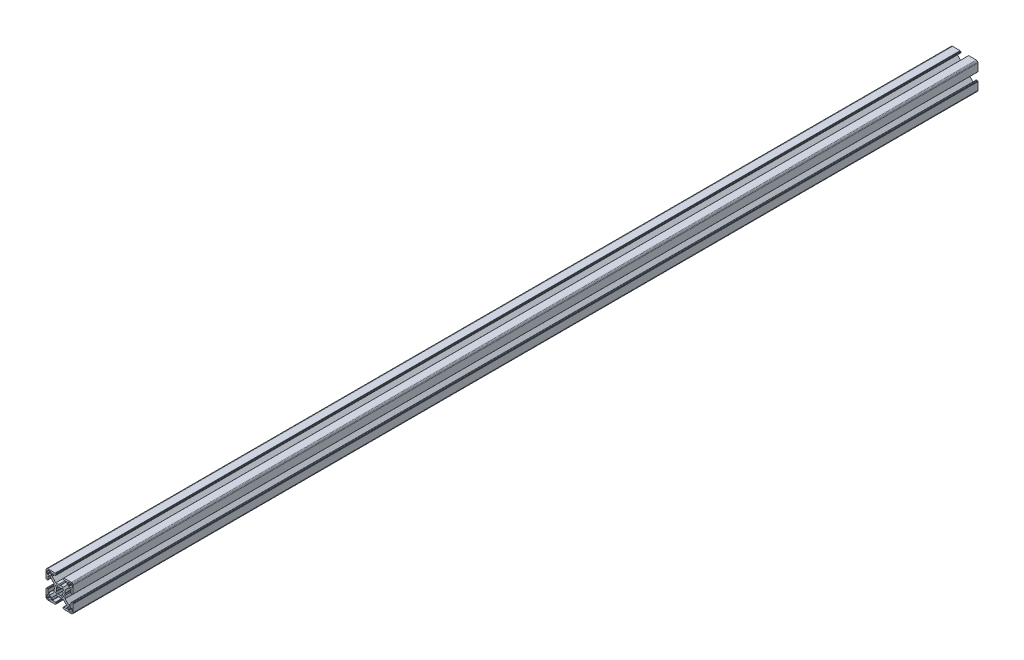
SolidWorks part; units mm, degrees
ref_plane "Front Plane" through (0, 0, 0) normal (0, 0, 1) x (1, 0, 0)
ref_plane "Top Plane" through (0, 0, 0) normal (0, 1, 0) x (1, 0, 0)
ref_plane "Right Plane" through (0, 0, 0) normal (1, 0, 0) x (0, 0, -1)
ref_plane "Plane1" through (0, 0, 0) normal (0, 0, 1) x (1, 0, 0)
sketch "Sketch1" plane through (0, 0, 0) normal (0, 0, 1) x (1, 0, 0)
  line L0 (28.3473, 29.9696) -> (28, 30)
  line L1 (28, 30) -> (19.75, 30)
  line L2 (19.75, 30) -> (19.7153, 29.997)
  line L3 (19.7153, 29.997) -> (19.6816, 29.9879)
  line L4 (19.6816, 29.9879) -> (19.65, 29.9732)
  line L5 (19.65, 29.9732) -> (19.6214, 29.9532)
  line L6 (19.6214, 29.9532) -> (19.5968, 29.9286)
  line L7 (19.5968, 29.9286) -> (19.5768, 29.9)
  line L8 (19.5768, 29.9) -> (19.5621, 29.8684)
  line L9 (19.5621, 29.8684) -> (19.553, 29.8347)
  line L10 (19.553, 29.8347) -> (19.55, 29.8)
  line L11 (19.55, 29.8) -> (19.55, 29.7)
  line L12 (19.55, 29.7) -> (19.547, 29.6653)
  line L13 (19.547, 29.6653) -> (19.5379, 29.6316)
  line L14 (19.5379, 29.6316) -> (19.5232, 29.6)
  line L15 (19.5232, 29.6) -> (19.5032, 29.5714)
  line L16 (19.5032, 29.5714) -> (19.4786, 29.5468)
  line L17 (19.4786, 29.5468) -> (19.45, 29.5268)
  line L18 (19.45, 29.5268) -> (19.4184, 29.5121)
  line L19 (19.4184, 29.5121) -> (19.3847, 29.503)
  line L20 (19.3847, 29.503) -> (19.35, 29.5)
  line L21 (19.35, 29.5) -> (19.25, 29.5)
  line L22 (19.25, 29.5) -> (19.2153, 29.497)
  line L23 (19.2153, 29.497) -> (19.1816, 29.4879)
  line L24 (19.1816, 29.4879) -> (19.15, 29.4732)
  line L25 (19.15, 29.4732) -> (19.1214, 29.4532)
  line L26 (19.1214, 29.4532) -> (19.0968, 29.4286)
  line L27 (19.0968, 29.4286) -> (19.0768, 29.4)
  line L28 (19.0768, 29.4) -> (19.0621, 29.3684)
  line L29 (19.0621, 29.3684) -> (19.053, 29.3347)
  line L30 (19.053, 29.3347) -> (19.05, 29.3)
  line L31 (19.05, 29.3) -> (19.05, 28.4)
  line L32 (19.05, 28.4) -> (19.0591, 28.2958)
  line L33 (19.0591, 28.2958) -> (19.0862, 28.1948)
  line L34 (19.0862, 28.1948) -> (19.1304, 28.1)
  line L35 (19.1304, 28.1) -> (19.1904, 28.0143)
  line L36 (19.1904, 28.0143) -> (19.2643, 27.9404)
  line L37 (19.2643, 27.9404) -> (19.35, 27.8804)
  line L38 (19.35, 27.8804) -> (19.4448, 27.8362)
  line L39 (19.4448, 27.8362) -> (19.5458, 27.8091)
  line L40 (19.5458, 27.8091) -> (19.65, 27.8)
  line L41 (19.65, 27.8) -> (23.05, 27.8)
  line L42 (23.05, 27.8) -> (23.0847, 27.7969)
  line L43 (23.0847, 27.7969) -> (23.1184, 27.7879)
  line L44 (23.1184, 27.7879) -> (23.15, 27.7732)
  line L45 (23.15, 27.7732) -> (23.1786, 27.7532)
  line L46 (23.1786, 27.7532) -> (23.2032, 27.7285)
  line L47 (23.2032, 27.7285) -> (23.2232, 27.7)
  line L48 (23.2232, 27.7) -> (23.2379, 27.6684)
  line L49 (23.2379, 27.6684) -> (23.247, 27.6347)
  line L50 (23.247, 27.6347) -> (23.25, 27.6)
  line L51 (23.25, 27.6) -> (23.25, 25.05)
  line L52 (23.25, 25.05) -> (19.2045, 21)
  line L53 (19.2045, 21) -> (15.9, 21)
  line L54 (15.9, 21) -> (15, 20.4848)
  line L55 (15, 20.4848) -> (14.1, 21)
  line L56 (14.1, 21) -> (10.7955, 21)
  line L57 (10.7955, 21) -> (7.9973, 23.8013)
  line L58 (7.9973, 23.8013) -> (6.75, 25.05)
  line L59 (6.75, 25.05) -> (6.75, 27.6)
  line L60 (6.75, 27.6) -> (6.753, 27.6347)
  line L61 (6.753, 27.6347) -> (6.7621, 27.6684)
  line L62 (6.7621, 27.6684) -> (6.7768, 27.7)
  line L63 (6.7768, 27.7) -> (6.7968, 27.7285)
  line L64 (6.7968, 27.7285) -> (6.8215, 27.7532)
  line L65 (6.8215, 27.7532) -> (6.85, 27.7732)
  line L66 (6.85, 27.7732) -> (6.8816, 27.7879)
  line L67 (6.8816, 27.7879) -> (6.9153, 27.7969)
  line L68 (6.9153, 27.7969) -> (6.95, 27.8)
  line L69 (6.95, 27.8) -> (10.35, 27.8)
  line L70 (10.35, 27.8) -> (10.4542, 27.8091)
  line L71 (10.4542, 27.8091) -> (10.5552, 27.8362)
  line L72 (10.5552, 27.8362) -> (10.65, 27.8804)
  line L73 (10.65, 27.8804) -> (10.7357, 27.9404)
  line L74 (10.7357, 27.9404) -> (10.8096, 28.0143)
  line L75 (10.8096, 28.0143) -> (10.8696, 28.1)
  line L76 (10.8696, 28.1) -> (10.9138, 28.1948)
  line L77 (10.9138, 28.1948) -> (10.9409, 28.2958)
  line L78 (10.9409, 28.2958) -> (10.95, 28.4)
  line L79 (10.95, 28.4) -> (10.95, 29.3)
  line L80 (10.95, 29.3) -> (10.947, 29.3347)
  line L81 (10.947, 29.3347) -> (10.938, 29.3684)
  line L82 (10.938, 29.3684) -> (10.9232, 29.4)
  line L83 (10.9232, 29.4) -> (10.9032, 29.4286)
  line L84 (10.9032, 29.4286) -> (10.8786, 29.4532)
  line L85 (10.8786, 29.4532) -> (10.85, 29.4732)
  line L86 (10.85, 29.4732) -> (10.8184, 29.4879)
  line L87 (10.8184, 29.4879) -> (10.7847, 29.497)
  line L88 (10.7847, 29.497) -> (10.75, 29.5)
  line L89 (10.75, 29.5) -> (10.65, 29.5)
  line L90 (10.65, 29.5) -> (10.6153, 29.503)
  line L91 (10.6153, 29.503) -> (10.5816, 29.5121)
  line L92 (10.5816, 29.5121) -> (10.55, 29.5268)
  line L93 (10.55, 29.5268) -> (10.5214, 29.5468)
  line L94 (10.5214, 29.5468) -> (10.4968, 29.5714)
  line L95 (10.4968, 29.5714) -> (10.4768, 29.6)
  line L96 (10.4768, 29.6) -> (10.4621, 29.6316)
  line L97 (10.4621, 29.6316) -> (10.453, 29.6653)
  line L98 (10.453, 29.6653) -> (10.45, 29.7)
  line L99 (10.45, 29.7) -> (10.45, 29.8)
  line L100 (10.45, 29.8) -> (10.447, 29.8347)
  line L101 (10.447, 29.8347) -> (10.4379, 29.8684)
  line L102 (10.4379, 29.8684) -> (10.4232, 29.9)
  line L103 (10.4232, 29.9) -> (10.4032, 29.9286)
  line L104 (10.4032, 29.9286) -> (10.3786, 29.9532)
  line L105 (10.3786, 29.9532) -> (10.35, 29.9732)
  line L106 (10.35, 29.9732) -> (10.3184, 29.9879)
  line L107 (10.3184, 29.9879) -> (10.2847, 29.997)
  line L108 (10.2847, 29.997) -> (10.25, 30)
  line L109 (10.25, 30) -> (2, 30)
  line L110 (2, 30) -> (1.6527, 29.9696)
  line L111 (1.6527, 29.9696) -> (1.316, 29.8794)
  line L112 (1.316, 29.8794) -> (1, 29.7321)
  line L113 (1, 29.7321) -> (0.7144, 29.5321)
  line L114 (0.7144, 29.5321) -> (0.4679, 29.2856)
  line L115 (0.4679, 29.2856) -> (0.2679, 29)
  line L116 (0.2679, 29) -> (0.1206, 28.684)
  line L117 (0.1206, 28.684) -> (0.0304, 28.3473)
  line L118 (0.0304, 28.3473) -> (0, 28)
  line L119 (0, 28) -> (0, 19.75)
  line L120 (0, 19.75) -> (0.003, 19.7153)
  line L121 (0.003, 19.7153) -> (0.0121, 19.6816)
  line L122 (0.0121, 19.6816) -> (0.0268, 19.65)
  line L123 (0.0268, 19.65) -> (0.0468, 19.6214)
  line L124 (0.0468, 19.6214) -> (0.0714, 19.5968)
  line L125 (0.0714, 19.5968) -> (0.1, 19.5768)
  line L126 (0.1, 19.5768) -> (0.1316, 19.5621)
  line L127 (0.1316, 19.5621) -> (0.1653, 19.553)
  line L128 (0.1653, 19.553) -> (0.2, 19.55)
  line L129 (0.2, 19.55) -> (0.3, 19.55)
  line L130 (0.3, 19.55) -> (0.3347, 19.547)
  line L131 (0.3347, 19.547) -> (0.3684, 19.5379)
  line L132 (0.3684, 19.5379) -> (0.4, 19.5232)
  line L133 (0.4, 19.5232) -> (0.4286, 19.5032)
  line L134 (0.4286, 19.5032) -> (0.4532, 19.4786)
  line L135 (0.4532, 19.4786) -> (0.4732, 19.45)
  line L136 (0.4732, 19.45) -> (0.4879, 19.4184)
  line L137 (0.4879, 19.4184) -> (0.497, 19.3847)
  line L138 (0.497, 19.3847) -> (0.5, 19.35)
  line L139 (0.5, 19.35) -> (0.5, 19.25)
  line L140 (0.5, 19.25) -> (0.503, 19.2153)
  line L141 (0.503, 19.2153) -> (0.5121, 19.1816)
  line L142 (0.5121, 19.1816) -> (0.5268, 19.15)
  line L143 (0.5268, 19.15) -> (0.5468, 19.1214)
  line L144 (0.5468, 19.1214) -> (0.5714, 19.0968)
  line L145 (0.5714, 19.0968) -> (0.6, 19.0768)
  line L146 (0.6, 19.0768) -> (0.6316, 19.0621)
  line L147 (0.6316, 19.0621) -> (0.6653, 19.053)
  line L148 (0.6653, 19.053) -> (0.7, 19.05)
  line L149 (0.7, 19.05) -> (1.6, 19.05)
  line L150 (1.6, 19.05) -> (1.7042, 19.0591)
  line L151 (1.7042, 19.0591) -> (1.8052, 19.0862)
  line L152 (1.8052, 19.0862) -> (1.9, 19.1304)
  line L153 (1.9, 19.1304) -> (1.9857, 19.1904)
  line L154 (1.9857, 19.1904) -> (2.0596, 19.2643)
  line L155 (2.0596, 19.2643) -> (2.1196, 19.35)
  line L156 (2.1196, 19.35) -> (2.1638, 19.4448)
  line L157 (2.1638, 19.4448) -> (2.1909, 19.5458)
  line L158 (2.1909, 19.5458) -> (2.2, 19.65)
  line L159 (2.2, 19.65) -> (2.2, 23.05)
  line L160 (2.2, 23.05) -> (2.203, 23.0847)
  line L161 (2.203, 23.0847) -> (2.2121, 23.1184)
  line L162 (2.2121, 23.1184) -> (2.2268, 23.15)
  line L163 (2.2268, 23.15) -> (2.2468, 23.1786)
  line L164 (2.2468, 23.1786) -> (2.2714, 23.2032)
  line L165 (2.2714, 23.2032) -> (2.3, 23.2232)
  line L166 (2.3, 23.2232) -> (2.3316, 23.2379)
  line L167 (2.3316, 23.2379) -> (2.3653, 23.247)
  line L168 (2.3653, 23.247) -> (2.4, 23.25)
  line L169 (2.4, 23.25) -> (4.95, 23.25)
  line L170 (4.95, 23.25) -> (7.9973, 20.2027)
  line L171 (7.9973, 20.2027) -> (8.9955, 19.2045)
  line L172 (8.9955, 19.2045) -> (8.9955, 15.9)
  line L173 (8.9955, 15.9) -> (9.5151, 15)
  line L174 (9.5151, 15) -> (8.9955, 14.1)
  line L175 (8.9955, 14.1) -> (8.9955, 10.7955)
  line L176 (8.9955, 10.7955) -> (4.95, 6.75)
  line L177 (4.95, 6.75) -> (2.4, 6.75)
  line L178 (2.4, 6.75) -> (2.3653, 6.753)
  line L179 (2.3653, 6.753) -> (2.3316, 6.7621)
  line L180 (2.3316, 6.7621) -> (2.3, 6.7768)
  line L181 (2.3, 6.7768) -> (2.2714, 6.7968)
  line L182 (2.2714, 6.7968) -> (2.2468, 6.8214)
  line L183 (2.2468, 6.8214) -> (2.2268, 6.85)
  line L184 (2.2268, 6.85) -> (2.2121, 6.8816)
  line L185 (2.2121, 6.8816) -> (2.203, 6.9153)
  line L186 (2.203, 6.9153) -> (2.2, 6.95)
  line L187 (2.2, 6.95) -> (2.2, 10.35)
  line L188 (2.2, 10.35) -> (2.1909, 10.4542)
  line L189 (2.1909, 10.4542) -> (2.1638, 10.5552)
  line L190 (2.1638, 10.5552) -> (2.1196, 10.65)
  line L191 (2.1196, 10.65) -> (2.0596, 10.7357)
  line L192 (2.0596, 10.7357) -> (1.9857, 10.8096)
  line L193 (1.9857, 10.8096) -> (1.9, 10.8696)
  line L194 (1.9, 10.8696) -> (1.8052, 10.9138)
  line L195 (1.8052, 10.9138) -> (1.7042, 10.9409)
  line L196 (1.7042, 10.9409) -> (1.6, 10.95)
  line L197 (1.6, 10.95) -> (0.7, 10.95)
  line L198 (0.7, 10.95) -> (0.6653, 10.9469)
  line L199 (0.6653, 10.9469) -> (0.6316, 10.9379)
  line L200 (0.6316, 10.9379) -> (0.6, 10.9232)
  line L201 (0.6, 10.9232) -> (0.5715, 10.9032)
  line L202 (0.5715, 10.9032) -> (0.5468, 10.8785)
  line L203 (0.5468, 10.8785) -> (0.5268, 10.85)
  line L204 (0.5268, 10.85) -> (0.5121, 10.8184)
  line L205 (0.5121, 10.8184) -> (0.503, 10.7847)
  line L206 (0.503, 10.7847) -> (0.5, 10.75)
  line L207 (0.5, 10.75) -> (0.5, 10.65)
  line L208 (0.5, 10.65) -> (0.497, 10.6153)
  line L209 (0.497, 10.6153) -> (0.4879, 10.5816)
  line L210 (0.4879, 10.5816) -> (0.4732, 10.55)
  line L211 (0.4732, 10.55) -> (0.4532, 10.5214)
  line L212 (0.4532, 10.5214) -> (0.4286, 10.4968)
  line L213 (0.4286, 10.4968) -> (0.4, 10.4768)
  line L214 (0.4, 10.4768) -> (0.3684, 10.4621)
  line L215 (0.3684, 10.4621) -> (0.3347, 10.453)
  line L216 (0.3347, 10.453) -> (0.3, 10.45)
  line L217 (0.3, 10.45) -> (0.2, 10.45)
  line L218 (0.2, 10.45) -> (0.1653, 10.447)
  line L219 (0.1653, 10.447) -> (0.1316, 10.4379)
  line L220 (0.1316, 10.4379) -> (0.1, 10.4232)
  line L221 (0.1, 10.4232) -> (0.0714, 10.4032)
  line L222 (0.0714, 10.4032) -> (0.0468, 10.3786)
  line L223 (0.0468, 10.3786) -> (0.0268, 10.35)
  line L224 (0.0268, 10.35) -> (0.0121, 10.3184)
  line L225 (0.0121, 10.3184) -> (0.003, 10.2847)
  line L226 (0.003, 10.2847) -> (0, 10.25)
  line L227 (0, 10.25) -> (0, 2)
  line L228 (0, 2) -> (0.0304, 1.6527)
  line L229 (0.0304, 1.6527) -> (0.1206, 1.316)
  line L230 (0.1206, 1.316) -> (0.2679, 1)
  line L231 (0.2679, 1) -> (0.4679, 0.7144)
  line L232 (0.4679, 0.7144) -> (0.7144, 0.4679)
  line L233 (0.7144, 0.4679) -> (1, 0.2679)
  line L234 (1, 0.2679) -> (1.316, 0.1206)
  line L235 (1.316, 0.1206) -> (1.6527, 0.0304)
  line L236 (1.6527, 0.0304) -> (2, 0)
  line L237 (2, 0) -> (10.25, 0)
  line L238 (10.25, 0) -> (10.2847, 0.003)
  line L239 (10.2847, 0.003) -> (10.3184, 0.0121)
  line L240 (10.3184, 0.0121) -> (10.35, 0.0268)
  line L241 (10.35, 0.0268) -> (10.3786, 0.0468)
  line L242 (10.3786, 0.0468) -> (10.4032, 0.0714)
  line L243 (10.4032, 0.0714) -> (10.4232, 0.1)
  line L244 (10.4232, 0.1) -> (10.4379, 0.1316)
  line L245 (10.4379, 0.1316) -> (10.447, 0.1653)
  line L246 (10.447, 0.1653) -> (10.45, 0.2)
  line L247 (10.45, 0.2) -> (10.45, 0.3)
  line L248 (10.45, 0.3) -> (10.453, 0.3347)
  line L249 (10.453, 0.3347) -> (10.4621, 0.3684)
  line L250 (10.4621, 0.3684) -> (10.4768, 0.4)
  line L251 (10.4768, 0.4) -> (10.4968, 0.4286)
  line L252 (10.4968, 0.4286) -> (10.5214, 0.4532)
  line L253 (10.5214, 0.4532) -> (10.55, 0.4732)
  line L254 (10.55, 0.4732) -> (10.5816, 0.4879)
  line L255 (10.5816, 0.4879) -> (10.6153, 0.497)
  line L256 (10.6153, 0.497) -> (10.65, 0.5)
  line L257 (10.65, 0.5) -> (10.75, 0.5)
  line L258 (10.75, 0.5) -> (10.7847, 0.503)
  line L259 (10.7847, 0.503) -> (10.8184, 0.5121)
  line L260 (10.8184, 0.5121) -> (10.85, 0.5268)
  line L261 (10.85, 0.5268) -> (10.8785, 0.5468)
  line L262 (10.8785, 0.5468) -> (10.9032, 0.5715)
  line L263 (10.9032, 0.5715) -> (10.9232, 0.6)
  line L264 (10.9232, 0.6) -> (10.9379, 0.6316)
  line L265 (10.9379, 0.6316) -> (10.9469, 0.6653)
  line L266 (10.9469, 0.6653) -> (10.95, 0.7)
  line L267 (10.95, 0.7) -> (10.95, 1.6)
  line L268 (10.95, 1.6) -> (10.9409, 1.7042)
  line L269 (10.9409, 1.7042) -> (10.9138, 1.8052)
  line L270 (10.9138, 1.8052) -> (10.8696, 1.9)
  line L271 (10.8696, 1.9) -> (10.8096, 1.9857)
  line L272 (10.8096, 1.9857) -> (10.7357, 2.0596)
  line L273 (10.7357, 2.0596) -> (10.65, 2.1196)
  line L274 (10.65, 2.1196) -> (10.5552, 2.1638)
  line L275 (10.5552, 2.1638) -> (10.4542, 2.1909)
  line L276 (10.4542, 2.1909) -> (10.35, 2.2)
  line L277 (10.35, 2.2) -> (6.95, 2.2)
  line L278 (6.95, 2.2) -> (6.9153, 2.203)
  line L279 (6.9153, 2.203) -> (6.8816, 2.212)
  line L280 (6.8816, 2.212) -> (6.85, 2.2268)
  line L281 (6.85, 2.2268) -> (6.8215, 2.2468)
  line L282 (6.8215, 2.2468) -> (6.7968, 2.2714)
  line L283 (6.7968, 2.2714) -> (6.7768, 2.3)
  line L284 (6.7768, 2.3) -> (6.7621, 2.3316)
  line L285 (6.7621, 2.3316) -> (6.753, 2.3653)
  line L286 (6.753, 2.3653) -> (6.75, 2.4)
  line L287 (6.75, 2.4) -> (6.75, 4.95)
  line L288 (6.75, 4.95) -> (9.7875, 7.9908)
  line L289 (9.7875, 7.9908) -> (10.7955, 9)
  line L290 (10.7955, 9) -> (14.1, 9)
  line L291 (14.1, 9) -> (15, 9.5151)
  line L292 (15, 9.5151) -> (15.9, 9)
  line L293 (15.9, 9) -> (19.2045, 9)
  line L294 (19.2045, 9) -> (20.2126, 7.9908)
  line L295 (20.2126, 7.9908) -> (23.25, 4.95)
  line L296 (23.25, 4.95) -> (23.25, 2.4)
  line L297 (23.25, 2.4) -> (23.247, 2.3653)
  line L298 (23.247, 2.3653) -> (23.2379, 2.3316)
  line L299 (23.2379, 2.3316) -> (23.2232, 2.3)
  line L300 (23.2232, 2.3) -> (23.2032, 2.2714)
  line L301 (23.2032, 2.2714) -> (23.1786, 2.2468)
  line L302 (23.1786, 2.2468) -> (23.15, 2.2268)
  line L303 (23.15, 2.2268) -> (23.1184, 2.212)
  line L304 (23.1184, 2.212) -> (23.0847, 2.203)
  line L305 (23.0847, 2.203) -> (23.05, 2.2)
  line L306 (23.05, 2.2) -> (19.65, 2.2)
  line L307 (19.65, 2.2) -> (19.5458, 2.1909)
  line L308 (19.5458, 2.1909) -> (19.4448, 2.1638)
  line L309 (19.4448, 2.1638) -> (19.35, 2.1196)
  line L310 (19.35, 2.1196) -> (19.2643, 2.0596)
  line L311 (19.2643, 2.0596) -> (19.1904, 1.9857)
  line L312 (19.1904, 1.9857) -> (19.1304, 1.9)
  line L313 (19.1304, 1.9) -> (19.0862, 1.8052)
  line L314 (19.0862, 1.8052) -> (19.0591, 1.7042)
  line L315 (19.0591, 1.7042) -> (19.05, 1.6)
  line L316 (19.05, 1.6) -> (19.05, 0.7)
  line L317 (19.05, 0.7) -> (19.053, 0.6653)
  line L318 (19.053, 0.6653) -> (19.0621, 0.6316)
  line L319 (19.0621, 0.6316) -> (19.0768, 0.6)
  line L320 (19.0768, 0.6) -> (19.0968, 0.5714)
  line L321 (19.0968, 0.5714) -> (19.1214, 0.5468)
  line L322 (19.1214, 0.5468) -> (19.15, 0.5268)
  line L323 (19.15, 0.5268) -> (19.1816, 0.5121)
  line L324 (19.1816, 0.5121) -> (19.2153, 0.503)
  line L325 (19.2153, 0.503) -> (19.25, 0.5)
  line L326 (19.25, 0.5) -> (19.35, 0.5)
  line L327 (19.35, 0.5) -> (19.3847, 0.497)
  line L328 (19.3847, 0.497) -> (19.4184, 0.4879)
  line L329 (19.4184, 0.4879) -> (19.45, 0.4732)
  line L330 (19.45, 0.4732) -> (19.4786, 0.4532)
  line L331 (19.4786, 0.4532) -> (19.5032, 0.4286)
  line L332 (19.5032, 0.4286) -> (19.5232, 0.4)
  line L333 (19.5232, 0.4) -> (19.5379, 0.3684)
  line L334 (19.5379, 0.3684) -> (19.547, 0.3347)
  line L335 (19.547, 0.3347) -> (19.55, 0.3)
  line L336 (19.55, 0.3) -> (19.55, 0.2)
  line L337 (19.55, 0.2) -> (19.553, 0.1653)
  line L338 (19.553, 0.1653) -> (19.5621, 0.1316)
  line L339 (19.5621, 0.1316) -> (19.5768, 0.1)
  line L340 (19.5768, 0.1) -> (19.5968, 0.0714)
  line L341 (19.5968, 0.0714) -> (19.6214, 0.0468)
  line L342 (19.6214, 0.0468) -> (19.65, 0.0268)
  line L343 (19.65, 0.0268) -> (19.6816, 0.0121)
  line L344 (19.6816, 0.0121) -> (19.7153, 0.003)
  line L345 (19.7153, 0.003) -> (19.75, 0)
  line L346 (19.75, 0) -> (28, 0)
  line L347 (28, 0) -> (28.3473, 0.0304)
  line L348 (28.3473, 0.0304) -> (28.684, 0.1206)
  line L349 (28.684, 0.1206) -> (29, 0.2679)
  line L350 (29, 0.2679) -> (29.2856, 0.4679)
  line L351 (29.2856, 0.4679) -> (29.5321, 0.7144)
  line L352 (29.5321, 0.7144) -> (29.7321, 1)
  line L353 (29.7321, 1) -> (29.8794, 1.316)
  line L354 (29.8794, 1.316) -> (29.9696, 1.6527)
  line L355 (29.9696, 1.6527) -> (30, 2)
  line L356 (30, 2) -> (30, 10.25)
  line L357 (30, 10.25) -> (29.997, 10.2847)
  line L358 (29.997, 10.2847) -> (29.988, 10.3184)
  line L359 (29.988, 10.3184) -> (29.9732, 10.35)
  line L360 (29.9732, 10.35) -> (29.9532, 10.3785)
  line L361 (29.9532, 10.3785) -> (29.9286, 10.4032)
  line L362 (29.9286, 10.4032) -> (29.9, 10.4232)
  line L363 (29.9, 10.4232) -> (29.8684, 10.4379)
  line L364 (29.8684, 10.4379) -> (29.8347, 10.447)
  line L365 (29.8347, 10.447) -> (29.8, 10.45)
  line L366 (29.8, 10.45) -> (29.7, 10.45)
  line L367 (29.7, 10.45) -> (29.6649, 10.4534)
  line L368 (29.6649, 10.4534) -> (29.6312, 10.4624)
  line L369 (29.6312, 10.4624) -> (29.5996, 10.4772)
  line L370 (29.5996, 10.4772) -> (29.5711, 10.4972)
  line L371 (29.5711, 10.4972) -> (29.5464, 10.5218)
  line L372 (29.5464, 10.5218) -> (29.5264, 10.5504)
  line L373 (29.5264, 10.5504) -> (29.5117, 10.582)
  line L374 (29.5117, 10.582) -> (29.5027, 10.6156)
  line L375 (29.5027, 10.6156) -> (29.4996, 10.6504)
  line L376 (29.4996, 10.6504) -> (29.4996, 10.7504)
  line L377 (29.4996, 10.7504) -> (29.497, 10.7847)
  line L378 (29.497, 10.7847) -> (29.4879, 10.8184)
  line L379 (29.4879, 10.8184) -> (29.4732, 10.85)
  line L380 (29.4732, 10.85) -> (29.4532, 10.8785)
  line L381 (29.4532, 10.8785) -> (29.4286, 10.9032)
  line L382 (29.4286, 10.9032) -> (29.4, 10.9232)
  line L383 (29.4, 10.9232) -> (29.3684, 10.9379)
  line L384 (29.3684, 10.9379) -> (29.3347, 10.9469)
  line L385 (29.3347, 10.9469) -> (29.3, 10.95)
  line L386 (29.3, 10.95) -> (28.4, 10.95)
  line L387 (28.4, 10.95) -> (28.2958, 10.9409)
  line L388 (28.2958, 10.9409) -> (28.1948, 10.9138)
  line L389 (28.1948, 10.9138) -> (28.1, 10.8696)
  line L390 (28.1, 10.8696) -> (28.0143, 10.8096)
  line L391 (28.0143, 10.8096) -> (27.9404, 10.7357)
  line L392 (27.9404, 10.7357) -> (27.8804, 10.65)
  line L393 (27.8804, 10.65) -> (27.8362, 10.5552)
  line L394 (27.8362, 10.5552) -> (27.8091, 10.4542)
  line L395 (27.8091, 10.4542) -> (27.8, 10.35)
  line L396 (27.8, 10.35) -> (27.8, 6.95)
  line L397 (27.8, 6.95) -> (27.797, 6.9153)
  line L398 (27.797, 6.9153) -> (27.7879, 6.8816)
  line L399 (27.7879, 6.8816) -> (27.7732, 6.85)
  line L400 (27.7732, 6.85) -> (27.7532, 6.8214)
  line L401 (27.7532, 6.8214) -> (27.7286, 6.7968)
  line L402 (27.7286, 6.7968) -> (27.7, 6.7768)
  line L403 (27.7, 6.7768) -> (27.6684, 6.7621)
  line L404 (27.6684, 6.7621) -> (27.6347, 6.753)
  line L405 (27.6347, 6.753) -> (27.6, 6.75)
  line L406 (27.6, 6.75) -> (25.05, 6.75)
  line L407 (25.05, 6.75) -> (23.8092, 7.9908)
  line L408 (23.8092, 7.9908) -> (21.0045, 10.7955)
  line L409 (21.0045, 10.7955) -> (21.0045, 14.1)
  line L410 (21.0045, 14.1) -> (20.4849, 15)
  line L411 (20.4849, 15) -> (21.0045, 15.9)
  line L412 (21.0045, 15.9) -> (21.0045, 19.2045)
  line L413 (21.0045, 19.2045) -> (25.05, 23.25)
  line L414 (25.05, 23.25) -> (27.6, 23.25)
  line L415 (27.6, 23.25) -> (27.6347, 23.247)
  line L416 (27.6347, 23.247) -> (27.6684, 23.2379)
  line L417 (27.6684, 23.2379) -> (27.7, 23.2232)
  line L418 (27.7, 23.2232) -> (27.7286, 23.2032)
  line L419 (27.7286, 23.2032) -> (27.7532, 23.1786)
  line L420 (27.7532, 23.1786) -> (27.7732, 23.15)
  line L421 (27.7732, 23.15) -> (27.7879, 23.1184)
  line L422 (27.7879, 23.1184) -> (27.797, 23.0847)
  line L423 (27.797, 23.0847) -> (27.8, 23.05)
  line L424 (27.8, 23.05) -> (27.8, 19.65)
  line L425 (27.8, 19.65) -> (27.8091, 19.5458)
  line L426 (27.8091, 19.5458) -> (27.8362, 19.4448)
  line L427 (27.8362, 19.4448) -> (27.8804, 19.35)
  line L428 (27.8804, 19.35) -> (27.9404, 19.2643)
  line L429 (27.9404, 19.2643) -> (28.0143, 19.1904)
  line L430 (28.0143, 19.1904) -> (28.1, 19.1304)
  line L431 (28.1, 19.1304) -> (28.1948, 19.0862)
  line L432 (28.1948, 19.0862) -> (28.2958, 19.0591)
  line L433 (28.2958, 19.0591) -> (28.4, 19.05)
  line L434 (28.4, 19.05) -> (29.3, 19.05)
  line L435 (29.3, 19.05) -> (29.3347, 19.053)
  line L436 (29.3347, 19.053) -> (29.3684, 19.0621)
  line L437 (29.3684, 19.0621) -> (29.4, 19.0768)
  line L438 (29.4, 19.0768) -> (29.4282, 19.0971)
  line L439 (29.4282, 19.0971) -> (29.4528, 19.1218)
  line L440 (29.4528, 19.1218) -> (29.4728, 19.1504)
  line L441 (29.4728, 19.1504) -> (29.4876, 19.182)
  line L442 (29.4876, 19.182) -> (29.4966, 19.2156)
  line L443 (29.4966, 19.2156) -> (29.4996, 19.2504)
  line L444 (29.4996, 19.2504) -> (29.4996, 19.3504)
  line L445 (29.4996, 19.3504) -> (29.5027, 19.3851)
  line L446 (29.5027, 19.3851) -> (29.5117, 19.4188)
  line L447 (29.5117, 19.4188) -> (29.5264, 19.4504)
  line L448 (29.5264, 19.4504) -> (29.5464, 19.4789)
  line L449 (29.5464, 19.4789) -> (29.5711, 19.5036)
  line L450 (29.5711, 19.5036) -> (29.5996, 19.5236)
  line L451 (29.5996, 19.5236) -> (29.6312, 19.5383)
  line L452 (29.6312, 19.5383) -> (29.6649, 19.5473)
  line L453 (29.6649, 19.5473) -> (29.7, 19.55)
  line L454 (29.7, 19.55) -> (29.8, 19.55)
  line L455 (29.8, 19.55) -> (29.8347, 19.553)
  line L456 (29.8347, 19.553) -> (29.8684, 19.5621)
  line L457 (29.8684, 19.5621) -> (29.9, 19.5768)
  line L458 (29.9, 19.5768) -> (29.9286, 19.5968)
  line L459 (29.9286, 19.5968) -> (29.9532, 19.6214)
  line L460 (29.9532, 19.6214) -> (29.9732, 19.65)
  line L461 (29.9732, 19.65) -> (29.9879, 19.6816)
  line L462 (29.9879, 19.6816) -> (29.997, 19.7153)
  line L463 (29.997, 19.7153) -> (30, 19.75)
  line L464 (30, 19.75) -> (30, 28)
  line L465 (30, 28) -> (29.9696, 28.3473)
  line L466 (29.9696, 28.3473) -> (29.8794, 28.684)
  line L467 (29.8794, 28.684) -> (29.7321, 29)
  line L468 (29.7321, 29) -> (29.5321, 29.2856)
  line L469 (29.5321, 29.2856) -> (29.2856, 29.5321)
  line L470 (29.2856, 29.5321) -> (29, 29.7321)
  line L471 (29, 29.7321) -> (28.684, 29.8794)
  line L472 (28.684, 29.8794) -> (28.3473, 29.9696)
  line L473 (1.3, 25.5) -> (1.3, 27.7)
  line L474 (1.3, 27.7) -> (1.3123, 27.8564)
  line L475 (1.3123, 27.8564) -> (1.3489, 28.009)
  line L476 (1.3489, 28.009) -> (1.409, 28.154)
  line L477 (1.409, 28.154) -> (1.491, 28.2878)
  line L478 (1.491, 28.2878) -> (1.5929, 28.4071)
  line L479 (1.5929, 28.4071) -> (1.7122, 28.509)
  line L480 (1.7122, 28.509) -> (1.846, 28.591)
  line L481 (1.846, 28.591) -> (1.991, 28.6511)
  line L482 (1.991, 28.6511) -> (2.1436, 28.6877)
  line L483 (2.1436, 28.6877) -> (2.3, 28.7)
  line L484 (2.3, 28.7) -> (4.5, 28.7)
  line L485 (4.5, 28.7) -> (4.6564, 28.6877)
  line L486 (4.6564, 28.6877) -> (4.809, 28.6511)
  line L487 (4.809, 28.6511) -> (4.954, 28.591)
  line L488 (4.954, 28.591) -> (5.0878, 28.509)
  line L489 (5.0878, 28.509) -> (5.2071, 28.4071)
  line L490 (5.2071, 28.4071) -> (5.309, 28.2878)
  line L491 (5.309, 28.2878) -> (5.391, 28.154)
  line L492 (5.391, 28.154) -> (5.4511, 28.009)
  line L493 (5.4511, 28.009) -> (5.4877, 27.8564)
  line L494 (5.4877, 27.8564) -> (5.5, 27.7)
  line L495 (5.5, 27.7) -> (5.5, 25.5)
  line L496 (5.5, 25.5) -> (5.4877, 25.3436)
  line L497 (5.4877, 25.3436) -> (5.4511, 25.191)
  line L498 (5.4511, 25.191) -> (5.391, 25.046)
  line L499 (5.391, 25.046) -> (5.309, 24.9122)
  line L500 (5.309, 24.9122) -> (5.2071, 24.7929)
  line L501 (5.2071, 24.7929) -> (5.0878, 24.691)
  line L502 (5.0878, 24.691) -> (4.954, 24.609)
  line L503 (4.954, 24.609) -> (4.809, 24.5489)
  line L504 (4.809, 24.5489) -> (4.6564, 24.5123)
  line L505 (4.6564, 24.5123) -> (4.5, 24.5)
  line L506 (4.5, 24.5) -> (2.3, 24.5)
  line L507 (2.3, 24.5) -> (2.1436, 24.5123)
  line L508 (2.1436, 24.5123) -> (1.991, 24.5489)
  line L509 (1.991, 24.5489) -> (1.846, 24.609)
  line L510 (1.846, 24.609) -> (1.7122, 24.691)
  line L511 (1.7122, 24.691) -> (1.5929, 24.7929)
  line L512 (1.5929, 24.7929) -> (1.491, 24.9122)
  line L513 (1.491, 24.9122) -> (1.409, 25.046)
  line L514 (1.409, 25.046) -> (1.3489, 25.191)
  line L515 (1.3489, 25.191) -> (1.3123, 25.3436)
  line L516 (1.3123, 25.3436) -> (1.3, 25.5)
  line L517 (25.3436, 28.6877) -> (25.5, 28.7)
  line L518 (25.5, 28.7) -> (27.7, 28.7)
  line L519 (27.7, 28.7) -> (27.8564, 28.6877)
  line L520 (27.8564, 28.6877) -> (28.009, 28.6511)
  line L521 (28.009, 28.6511) -> (28.154, 28.591)
  line L522 (28.154, 28.591) -> (28.2878, 28.509)
  line L523 (28.2878, 28.509) -> (28.4071, 28.4071)
  line L524 (28.4071, 28.4071) -> (28.509, 28.2878)
  line L525 (28.509, 28.2878) -> (28.591, 28.154)
  line L526 (28.591, 28.154) -> (28.6511, 28.009)
  line L527 (28.6511, 28.009) -> (28.6877, 27.8564)
  line L528 (28.6877, 27.8564) -> (28.7, 27.7)
  line L529 (28.7, 27.7) -> (28.7, 25.5)
  line L530 (28.7, 25.5) -> (28.6877, 25.3436)
  line L531 (28.6877, 25.3436) -> (28.6511, 25.191)
  line L532 (28.6511, 25.191) -> (28.591, 25.046)
  line L533 (28.591, 25.046) -> (28.509, 24.9122)
  line L534 (28.509, 24.9122) -> (28.4071, 24.7929)
  line L535 (28.4071, 24.7929) -> (28.2878, 24.691)
  line L536 (28.2878, 24.691) -> (28.154, 24.609)
  line L537 (28.154, 24.609) -> (28.009, 24.5489)
  line L538 (28.009, 24.5489) -> (27.8564, 24.5123)
  line L539 (27.8564, 24.5123) -> (27.7, 24.5)
  line L540 (27.7, 24.5) -> (25.5, 24.5)
  line L541 (25.5, 24.5) -> (25.3436, 24.5123)
  line L542 (25.3436, 24.5123) -> (25.191, 24.5489)
  line L543 (25.191, 24.5489) -> (25.046, 24.609)
  line L544 (25.046, 24.609) -> (24.9122, 24.691)
  line L545 (24.9122, 24.691) -> (24.7929, 24.7929)
  line L546 (24.7929, 24.7929) -> (24.691, 24.9122)
  line L547 (24.691, 24.9122) -> (24.609, 25.046)
  line L548 (24.609, 25.046) -> (24.5489, 25.191)
  line L549 (24.5489, 25.191) -> (24.5123, 25.3436)
  line L550 (24.5123, 25.3436) -> (24.5, 25.5)
  line L551 (24.5, 25.5) -> (24.5, 27.7)
  line L552 (24.5, 27.7) -> (24.5123, 27.8564)
  line L553 (24.5123, 27.8564) -> (24.5489, 28.009)
  line L554 (24.5489, 28.009) -> (24.609, 28.154)
  line L555 (24.609, 28.154) -> (24.691, 28.2878)
  line L556 (24.691, 28.2878) -> (24.7929, 28.4071)
  line L557 (24.7929, 28.4071) -> (24.9122, 28.509)
  line L558 (24.9122, 28.509) -> (25.046, 28.591)
  line L559 (25.046, 28.591) -> (25.191, 28.6511)
  line L560 (25.191, 28.6511) -> (25.3436, 28.6877)
  line L561 (15, 18.65) -> (15.55, 18.6083)
  line L562 (15.55, 18.6083) -> (16.0875, 18.4842)
  line L563 (16.0875, 18.4842) -> (16.6001, 18.2806)
  line L564 (16.6001, 18.2806) -> (18.1359, 19.5184)
  line L565 (18.1359, 19.5184) -> (18.645, 19.1187)
  line L566 (18.645, 19.1187) -> (19.1036, 18.6621)
  line L567 (19.1036, 18.6621) -> (19.5053, 18.1547)
  line L568 (19.5053, 18.1547) -> (18.2806, 16.6001)
  line L569 (18.2806, 16.6001) -> (18.4842, 16.0875)
  line L570 (18.4842, 16.0875) -> (18.6083, 15.55)
  line L571 (18.6083, 15.55) -> (18.65, 15)
  line L572 (18.65, 15) -> (18.6083, 14.45)
  line L573 (18.6083, 14.45) -> (18.4842, 13.9125)
  line L574 (18.4842, 13.9125) -> (18.2806, 13.3999)
  line L575 (18.2806, 13.3999) -> (19.5053, 11.8453)
  line L576 (19.5053, 11.8453) -> (19.1036, 11.3379)
  line L577 (19.1036, 11.3379) -> (18.645, 10.8813)
  line L578 (18.645, 10.8813) -> (18.1359, 10.4816)
  line L579 (18.1359, 10.4816) -> (16.6001, 11.7194)
  line L580 (16.6001, 11.7194) -> (16.0875, 11.5158)
  line L581 (16.0875, 11.5158) -> (15.55, 11.3917)
  line L582 (15.55, 11.3917) -> (15, 11.35)
  line L583 (15, 11.35) -> (14.45, 11.3917)
  line L584 (14.45, 11.3917) -> (13.9125, 11.5158)
  line L585 (13.9125, 11.5158) -> (13.3999, 11.7194)
  line L586 (13.3999, 11.7194) -> (11.8641, 10.4816)
  line L587 (11.8641, 10.4816) -> (11.355, 10.8813)
  line L588 (11.355, 10.8813) -> (10.8964, 11.3379)
  line L589 (10.8964, 11.3379) -> (10.4947, 11.8453)
  line L590 (10.4947, 11.8453) -> (11.7194, 13.3999)
  line L591 (11.7194, 13.3999) -> (11.5158, 13.9125)
  line L592 (11.5158, 13.9125) -> (11.3917, 14.45)
  line L593 (11.3917, 14.45) -> (11.35, 15)
  line L594 (11.35, 15) -> (11.3917, 15.55)
  line L595 (11.3917, 15.55) -> (11.5158, 16.0875)
  line L596 (11.5158, 16.0875) -> (11.7194, 16.6001)
  line L597 (11.7194, 16.6001) -> (10.4947, 18.1547)
  line L598 (10.4947, 18.1547) -> (10.8964, 18.6621)
  line L599 (10.8964, 18.6621) -> (11.355, 19.1187)
  line L600 (11.355, 19.1187) -> (11.8641, 19.5184)
  line L601 (11.8641, 19.5184) -> (13.3999, 18.2806)
  line L602 (13.3999, 18.2806) -> (13.9125, 18.4842)
  line L603 (13.9125, 18.4842) -> (14.45, 18.6083)
  line L604 (14.45, 18.6083) -> (15, 18.65)
  line L605 (4.5, 1.3) -> (2.3, 1.3)
  line L606 (2.3, 1.3) -> (2.1436, 1.3123)
  line L607 (2.1436, 1.3123) -> (1.991, 1.3489)
  line L608 (1.991, 1.3489) -> (1.846, 1.409)
  line L609 (1.846, 1.409) -> (1.7122, 1.491)
  line L610 (1.7122, 1.491) -> (1.5929, 1.5929)
  line L611 (1.5929, 1.5929) -> (1.491, 1.7122)
  line L612 (1.491, 1.7122) -> (1.409, 1.846)
  line L613 (1.409, 1.846) -> (1.3489, 1.991)
  line L614 (1.3489, 1.991) -> (1.3123, 2.1436)
  line L615 (1.3123, 2.1436) -> (1.3, 2.3)
  line L616 (1.3, 2.3) -> (1.3, 4.5)
  line L617 (1.3, 4.5) -> (1.3123, 4.6564)
  line L618 (1.3123, 4.6564) -> (1.3489, 4.809)
  line L619 (1.3489, 4.809) -> (1.409, 4.954)
  line L620 (1.409, 4.954) -> (1.491, 5.0878)
  line L621 (1.491, 5.0878) -> (1.5929, 5.2071)
  line L622 (1.5929, 5.2071) -> (1.7122, 5.309)
  line L623 (1.7122, 5.309) -> (1.846, 5.391)
  line L624 (1.846, 5.391) -> (1.991, 5.4511)
  line L625 (1.991, 5.4511) -> (2.1436, 5.4877)
  line L626 (2.1436, 5.4877) -> (2.3, 5.5)
  line L627 (2.3, 5.5) -> (4.5, 5.5)
  line L628 (4.5, 5.5) -> (4.6564, 5.4877)
  line L629 (4.6564, 5.4877) -> (4.809, 5.4511)
  line L630 (4.809, 5.4511) -> (4.954, 5.391)
  line L631 (4.954, 5.391) -> (5.0878, 5.309)
  line L632 (5.0878, 5.309) -> (5.2071, 5.2071)
  line L633 (5.2071, 5.2071) -> (5.309, 5.0878)
  line L634 (5.309, 5.0878) -> (5.391, 4.954)
  line L635 (5.391, 4.954) -> (5.4511, 4.809)
  line L636 (5.4511, 4.809) -> (5.4877, 4.6564)
  line L637 (5.4877, 4.6564) -> (5.5, 4.5)
  line L638 (5.5, 4.5) -> (5.5, 2.3)
  line L639 (5.5, 2.3) -> (5.4877, 2.1436)
  line L640 (5.4877, 2.1436) -> (5.4511, 1.991)
  line L641 (5.4511, 1.991) -> (5.391, 1.846)
  line L642 (5.391, 1.846) -> (5.309, 1.7122)
  line L643 (5.309, 1.7122) -> (5.2071, 1.5929)
  line L644 (5.2071, 1.5929) -> (5.0878, 1.491)
  line L645 (5.0878, 1.491) -> (4.954, 1.409)
  line L646 (4.954, 1.409) -> (4.809, 1.3489)
  line L647 (4.809, 1.3489) -> (4.6564, 1.3123)
  line L648 (4.6564, 1.3123) -> (4.5, 1.3)
  line L649 (27.7, 1.3) -> (25.5, 1.3)
  line L650 (25.5, 1.3) -> (25.3436, 1.3123)
  line L651 (25.3436, 1.3123) -> (25.191, 1.3489)
  line L652 (25.191, 1.3489) -> (25.046, 1.409)
  line L653 (25.046, 1.409) -> (24.9122, 1.491)
  line L654 (24.9122, 1.491) -> (24.7929, 1.5929)
  line L655 (24.7929, 1.5929) -> (24.691, 1.7122)
  line L656 (24.691, 1.7122) -> (24.609, 1.846)
  line L657 (24.609, 1.846) -> (24.5489, 1.991)
  line L658 (24.5489, 1.991) -> (24.5123, 2.1436)
  line L659 (24.5123, 2.1436) -> (24.5, 2.3)
  line L660 (24.5, 2.3) -> (24.5, 4.5)
  line L661 (24.5, 4.5) -> (24.5123, 4.6564)
  line L662 (24.5123, 4.6564) -> (24.5489, 4.809)
  line L663 (24.5489, 4.809) -> (24.609, 4.954)
  line L664 (24.609, 4.954) -> (24.691, 5.0878)
  line L665 (24.691, 5.0878) -> (24.7929, 5.2071)
  line L666 (24.7929, 5.2071) -> (24.9122, 5.309)
  line L667 (24.9122, 5.309) -> (25.046, 5.391)
  line L668 (25.046, 5.391) -> (25.191, 5.4511)
  line L669 (25.191, 5.4511) -> (25.3436, 5.4877)
  line L670 (25.3436, 5.4877) -> (25.5, 5.5)
  line L671 (25.5, 5.5) -> (27.7, 5.5)
  line L672 (27.7, 5.5) -> (27.8564, 5.4877)
  line L673 (27.8564, 5.4877) -> (28.009, 5.4511)
  line L674 (28.009, 5.4511) -> (28.154, 5.391)
  line L675 (28.154, 5.391) -> (28.2878, 5.309)
  line L676 (28.2878, 5.309) -> (28.4071, 5.2071)
  line L677 (28.4071, 5.2071) -> (28.509, 5.0878)
  line L678 (28.509, 5.0878) -> (28.591, 4.954)
  line L679 (28.591, 4.954) -> (28.6511, 4.809)
  line L680 (28.6511, 4.809) -> (28.6877, 4.6564)
  line L681 (28.6877, 4.6564) -> (28.7, 4.5)
  line L682 (28.7, 4.5) -> (28.7, 2.3)
  line L683 (28.7, 2.3) -> (28.6877, 2.1436)
  line L684 (28.6877, 2.1436) -> (28.6511, 1.991)
  line L685 (28.6511, 1.991) -> (28.591, 1.846)
  line L686 (28.591, 1.846) -> (28.509, 1.7122)
  line L687 (28.509, 1.7122) -> (28.4071, 1.5929)
  line L688 (28.4071, 1.5929) -> (28.2878, 1.491)
  line L689 (28.2878, 1.491) -> (28.154, 1.409)
  line L690 (28.154, 1.409) -> (28.009, 1.3489)
  line L691 (28.009, 1.3489) -> (27.8564, 1.3123)
  line L692 (27.8564, 1.3123) -> (27.7, 1.3)
extrude "Boss-Extrude1" add sketch "Sketch1" against normal blind 1000
